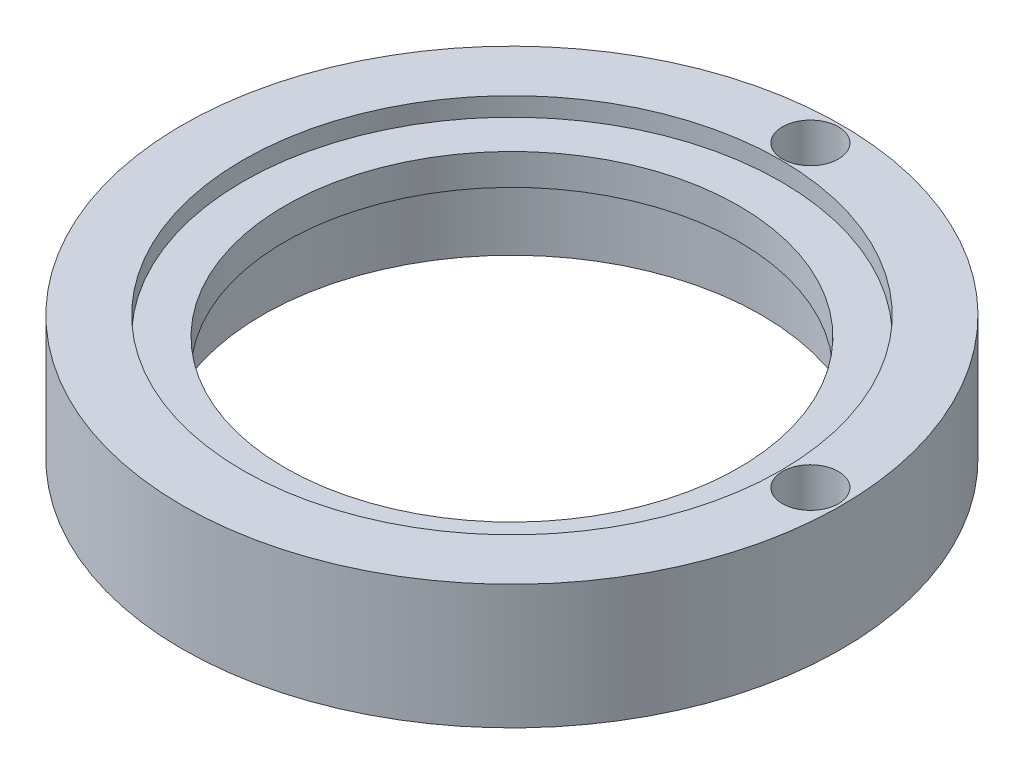
SolidWorks part; units mm, degrees
ref_plane "Front Plane" through (0, 0, 0) normal (0, 0, 1) x (1, 0, 0)
ref_plane "Top Plane" through (0, 0, 0) normal (0, 1, 0) x (1, 0, 0)
ref_plane "Right Plane" through (0, 0, 0) normal (1, 0, 0) x (0, 0, -1)
sketch "Sketch1" plane through (0, 0, 0) normal (0, 1, 0) x (1, 0, 0)
  circle A0 centre (0, 0) radius 36.5
  circle A1 centre (0, 0) radius 53
  dimension "D1" = 73
  dimension "D2" = 106
extrude "Boss-Extrude1" add sketch "Sketch1" along normal blind 20
sketch "Sketch2" plane through (0, 20, 0) normal (0, 1, 0) x (1, 0, 0)
  circle A0 centre (0, 0) radius 43.25
  dimension "D1" = 86.5
extrude "LED-ring" cut sketch "Sketch2" against normal blind 3
sketch "Sketch3" plane through (0, 0, 0) normal (0, -1, 0) x (1, 0, 0)
  circle A0 centre (0, 0) radius 40.1
  dimension "D1" = 80.2
extrude "spindle" cut sketch "Sketch3" against normal offset from surface (12 mm away) 5 up to face at (0, 17, 36.5)
sketch "Sketch4" plane through (0, 20, 0) normal (0, 1, 0) x (1, 0, 0)
  circle A0 centre (0, 48) radius 4.5
  circle A1 centre (48, 0) radius 4.5
  dimension "D1" = 9
  dimension "D2" = 48
  dimension "D3" = 48
extrude "lasers" cut sketch "Sketch4" against normal through all
equation "\"D3@Sketch4\"=\"D2@Sketch4\""
